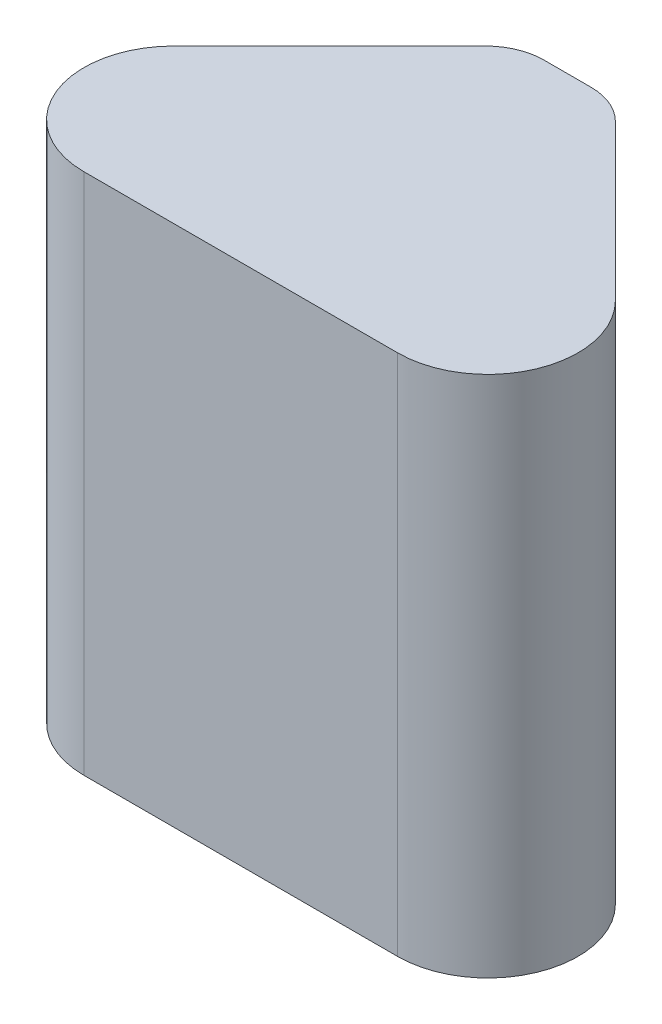
SolidWorks part; units mm, degrees
ref_plane "Front Plane" through (0, 0, 0) normal (0, 0, 1) x (1, 0, 0)
ref_plane "Top Plane" through (0, 0, 0) normal (0, 1, 0) x (1, 0, 0)
ref_plane "Right Plane" through (0, 0, 0) normal (1, 0, 0) x (0, 0, -1)
sketch "Sketch1" plane through (0, 0, 0) normal (0, 1, 0) x (1, 0, 0)
  line B0 (-0.8048, 185.2665) -> (-46.4992, 185.2665)
  line B1 (-86.9103, 168.5276) -> (-238.0777, 17.3602)
  line B2 (190.7737, 17.3602) -> (39.6063, 168.5276)
  line B3 (-176.114, -132.2335) -> (128.8099, -132.2335)
  arc B4 (-46.4992, 185.2665) -> (-86.9103, 168.5276) centre (-46.4992, 128.1165) ccw
  arc B5 (39.6063, 168.5276) -> (-0.8048, 185.2665) centre (-0.8048, 128.1165) ccw
  arc B6 (128.8099, -132.2335) -> (190.7737, 17.3602) centre (128.8099, -44.6035) ccw
  arc B7 (-238.0777, 17.3602) -> (-176.114, -132.2335) centre (-176.114, -44.6035) ccw
sketch_block_instance "insert sketch-1"
sketch_block "insert sketch"
extrude "Boss-Extrude1" add sketch "Sketch1" along normal blind 508
